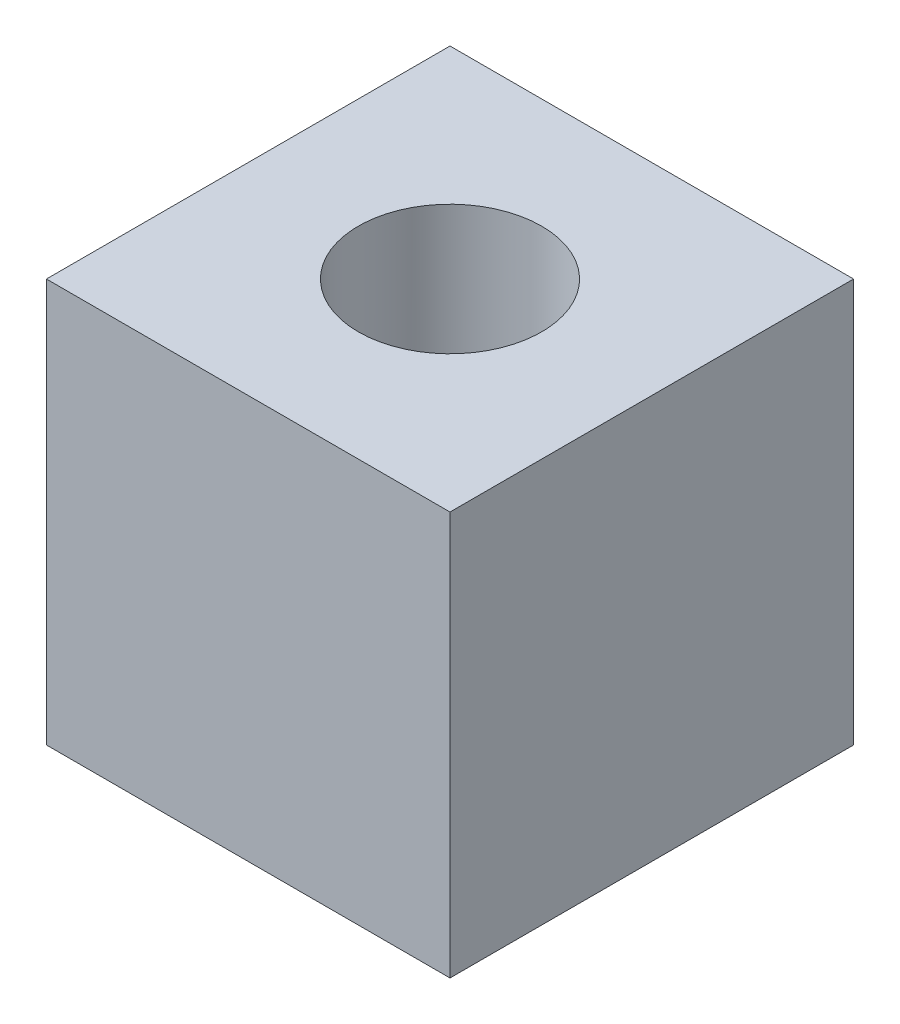
SolidWorks part; units mm, degrees
ref_plane "Front Plane" through (0, 0, 0) normal (0, 0, 1) x (1, 0, 0)
ref_plane "Top Plane" through (0, 0, 0) normal (0, 1, 0) x (1, 0, 0)
ref_plane "Right Plane" through (0, 0, 0) normal (1, 0, 0) x (0, 0, -1)
sketch "Sketch1" plane through (0, 0, 0) normal (0, 1, 0) x (1, 0, 0)
  line L1 (-6, -6) -> (6, -6)
  line L2 (-6, -6) -> (-6, 6)
  line L3 (-6, 6) -> (6, 6)
  line L4 (6, -6) -> (6, 6)
  line L5 (-6, -6) -> (6, 6) construction
  line L6 (-6, 6) -> (6, -6) construction
  circle A0 centre (0, 0) radius 2.725
  dimension "D1" = 5.45
  dimension "D2" = 12
extrude "Boss-Extrude1" add sketch "Sketch1" along normal blind 12
sketch "Sketch2" plane through (0, 0, 0) normal (0, -1, 0) x (1, 0, 0)
  circle A0 centre (0, 0) radius 2.25
  circle A1 centre (0, 0) radius 2.725 construction
  circle A2 centre (0, 0) radius 2.725
  dimension "D1" = 4.5
extrude "Boss-Extrude2" add sketch "Sketch2" against normal offset from surface (4 mm away) 8 up to face at (0, 12, 0)
